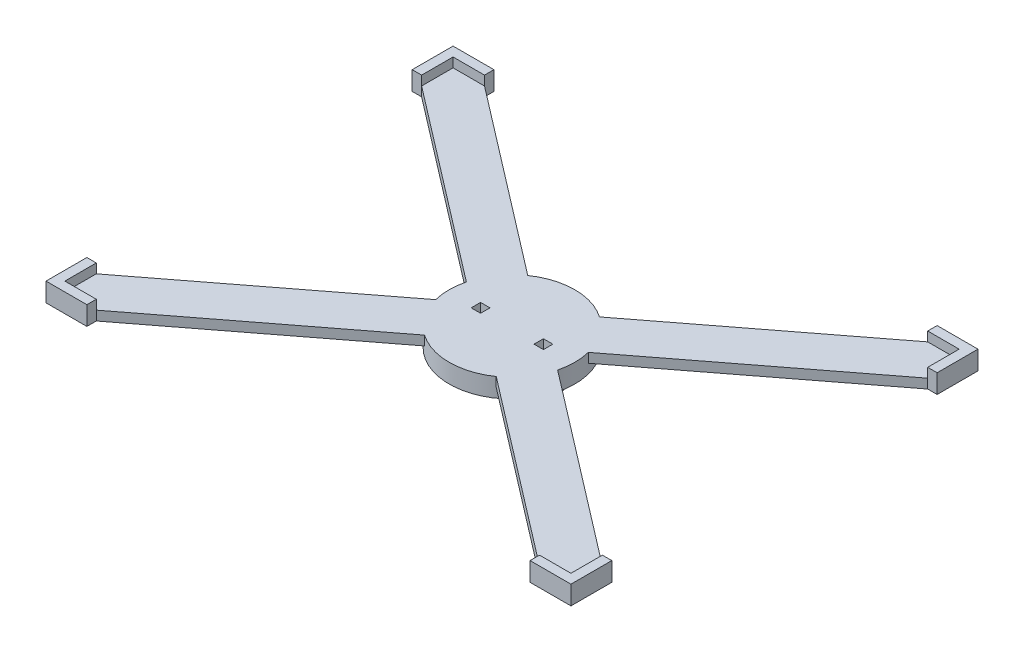
SolidWorks part; units mm, degrees
ref_plane "Alzado" through (0, 0, 0) normal (0, 0, 1) x (1, 0, 0)
ref_plane "Planta" through (0, 0, 0) normal (0, 1, 0) x (1, 0, 0)
ref_plane "Vista lateral" through (0, 0, 0) normal (1, 0, 0) x (0, 0, -1)
sketch "Croquis1" plane through (0, 0, 0) normal (0, 1, 0) x (1, 0, 0)
  line L0 (-161, 103.5) -> (-38.7919, 9.7565)
  line L1 (-40, 40) -> (40, 40) construction
  line L2 (-40, 40) -> (-40, -40) construction
  line L3 (-40, -40) -> (40, -40) construction
  line L4 (40, 40) -> (40, -40) construction
  line L5 (-40, 40) -> (40, -40) construction
  line L6 (-40, -40) -> (40, 40) construction
  line L7 (-161, 123.5) -> (161, 123.5) construction
  line L8 (-161, 123.5) -> (-161, -123.5) construction
  line L9 (-161, -123.5) -> (161, -123.5) construction
  line L10 (161, 123.5) -> (161, -123.5) construction
  line L11 (-161, 123.5) -> (161, -123.5) construction
  line L12 (-161, -123.5) -> (161, 123.5) construction
  line L13 (-161, 103.5) -> (-161, 123.5)
  line L14 (-161, 123.5) -> (-141, 123.5)
  line L15 (-141, 123.5) -> (-22.8238, 32.8493)
  line L16 (-38.7919, -9.7565) -> (-161, -103.5)
  line L17 (-161, -103.5) -> (-161, -123.5)
  line L18 (-161, -123.5) -> (-141, -123.5)
  line L19 (-141, -123.5) -> (-22.8238, -32.8493)
  line L20 (-38.7919, 9.7565) -> (-38.7919, -9.7565) construction
  line L21 (-22.8238, 32.8493) -> (-22.8238, -32.8493) construction
  line L22 (0, 40) -> (0, -40) construction
  line L23 (161, 123.5) -> (141, 123.5)
  line L24 (141, 123.5) -> (22.8238, 32.8493)
  line L25 (161, 103.5) -> (161, 123.5)
  line L26 (161, 103.5) -> (38.7919, 9.7565)
  line L27 (161, -123.5) -> (141, -123.5)
  line L28 (161, -103.5) -> (161, -123.5)
  line L29 (38.7919, -9.7565) -> (161, -103.5)
  line L30 (141, -123.5) -> (22.8238, -32.8493)
  circle A0 centre (0, 0) radius 40 construction
  arc A1 (-38.7919, 9.7565) -> (-38.7919, -9.7565) centre (0, 0) ccw
  arc A2 (-22.8238, 32.8493) -> (22.8238, 32.8493) centre (0, 0) cw
  arc A3 (22.8238, -32.8493) -> (-22.8238, -32.8493) centre (0, 0) cw
  arc A4 (38.7919, 9.7565) -> (38.7919, -9.7565) centre (0, 0) cw
  point P0 (0, 0)
  point P6 (0, 0)
  dimension "D1" = 80
  dimension "D2" = 80
  dimension "D3" = 322
  dimension "D4" = 247
  dimension "D5" = 20
extrude "Saliente-Extruir1" add sketch "Croquis1" along normal blind 6
sketch "Croquis4" plane through (0, 0, 0) normal (0, 1, 0) x (1, 0, 0)
  line L0 (-161, 103.5) -> (-161, 123.5)
  line L1 (-161, 123.5) -> (-141, 123.5)
  line L2 (-141, 123.5) -> (-141, 129.5)
  line L3 (-141, 129.5) -> (-167, 129.5)
  line L4 (-167, 129.5) -> (-167, 103.5)
  line L5 (-167, 103.5) -> (-161, 103.5)
  line L6 (-161, -103.5) -> (-161, -123.5)
  line L7 (-161, -123.5) -> (-141, -123.5)
  line L8 (-141, -123.5) -> (-141, -129.5)
  line L9 (-141, -129.5) -> (-167, -129.5)
  line L10 (-167, -129.5) -> (-167, -103.5)
  line L11 (-167, -103.5) -> (-161, -103.5)
  line L12 (0, 40) -> (0, -40) construction
  line L13 (167, -103.5) -> (161, -103.5)
  line L14 (167, -129.5) -> (167, -103.5)
  line L15 (141, -129.5) -> (167, -129.5)
  line L16 (141, -123.5) -> (141, -129.5)
  line L17 (161, -123.5) -> (141, -123.5)
  line L18 (161, -103.5) -> (161, -123.5)
  line L19 (167, 103.5) -> (161, 103.5)
  line L20 (167, 129.5) -> (167, 103.5)
  line L21 (141, 129.5) -> (167, 129.5)
  line L22 (141, 123.5) -> (141, 129.5)
  line L23 (161, 123.5) -> (141, 123.5)
  line L24 (161, 103.5) -> (161, 123.5)
  arc A0 (22.8238, 32.8493) -> (-22.8238, 32.8493) centre (0, 0) ccw construction
  arc A1 (-22.8238, -32.8493) -> (22.8238, -32.8493) centre (0, 0) ccw construction
  dimension "D1" = 6
  dimension "D2" = 6
  dimension "D3" = 6
  dimension "D4" = 6
extrude "Saliente-Extruir2" add sketch "Croquis4" along normal blind 12
sketch "Croquis7" plane through (0, 0, 0) normal (0, -1, 0) x (-1, 0, 0)
  circle A0 centre (0, 0) radius 40
  arc A1 (-38.7919, 9.7565) -> (-38.7919, -9.7565) centre (0, 0) ccw construction
extrude "Saliente-Extruir5" add sketch "Croquis7" along normal blind 6
sketch "Croquis5" plane through (0, -6, 0) normal (0, -1, 0) x (1, 0, 0)
  line L0 (13.25, 11) -> (-13.25, 11) construction
  line L1 (-10.25, 8) -> (10.25, 8) construction
  line L2 (-10.25, 8) -> (-10.25, -8) construction
  line L3 (-10.25, -8) -> (10.25, -8) construction
  line L4 (10.25, 8) -> (10.25, -8) construction
  line L5 (-10.25, 8) -> (10.25, -8) construction
  line L6 (-10.25, -8) -> (10.25, 8) construction
  line L7 (-13.25, 11) -> (-13.25, -11) construction
  line L8 (-13.25, -11) -> (13.25, -11) construction
  line L9 (13.25, -11) -> (13.25, -21) construction
  line L10 (13.25, -21) -> (-28.25, -21) construction
  line L11 (-28.25, -21) -> (-28.25, 21) construction
  line L12 (-28.25, 21) -> (13.25, 21) construction
  line L13 (13.25, 21) -> (13.25, 11) construction
  line L14 (0, 11) -> (0, 0) construction
  line L15 (0, 0) -> (0, -11) construction
  line L16 (13.25, 11) -> (28.25, 11) construction
  line L17 (-28.25, 21) -> (28.25, 21) construction
  line L18 (-28.25, 21) -> (-28.25, -21) construction
  line L19 (-28.25, -21) -> (28.25, -21) construction
  line L20 (28.25, 21) -> (28.25, -21) construction
  line L21 (-28.25, 21) -> (28.25, -21) construction
  line L22 (-28.25, -21) -> (28.25, 21) construction
  line L23 (28.25, 11) -> (28.25, 21) construction
  line L24 (28.25, 21) -> (13.25, 21) construction
  line L25 (13.25, -21) -> (28.25, -21) construction
  line L26 (28.25, -21) -> (28.25, -11) construction
  line L27 (28.25, -11) -> (13.25, -11) construction
  line L28 (-9, 7) -> (9, 7) construction
  line L29 (0, 7) -> (0, 0) construction
  line L30 (-9, 7) -> (9, 7) construction
  line L31 (-9, 7.5) -> (9, 7.5) construction
  line L32 (-9, 6.5) -> (9, 6.5) construction
  line L33 (-18.8961, 21) -> (18.8961, 21) construction
  line L34 (18.8961, -21) -> (-18.8961, -21)
  line L35 (-18.8961, 21) -> (-13.25, 21)
  line L36 (-13.25, 21) -> (-13.25, -11)
  line L37 (-13.25, -11) -> (13.25, -11)
  line L38 (13.25, -11) -> (13.25, 21)
  line L39 (13.25, 21) -> (18.8961, 21)
  line L40 (-8, -5.75) -> (8, -5.75) construction
  arc A0 (-9, 7.5) -> (-9, 6.5) centre (-9, 7) ccw construction
  arc A1 (9, 6.5) -> (9, 7.5) centre (9, 7) ccw construction
  arc A2 (-18.8961, 21) -> (-18.8961, -21) centre (0, 0) ccw
  arc A3 (18.8961, 21) -> (18.8961, -21) centre (0, 0) cw
  circle A4 centre (-8, -5.75) radius 1.75 construction
  circle A5 centre (8, -5.75) radius 1.75 construction
  point P0 (0, 0)
  point P26 (0, 7)
  dimension "D11" = 0.5
  dimension "D12" = 3.5
  dimension "D14" = 2.25
  dimension "D1" = 16
  dimension "D2" = 20.5
  dimension "D3" = 3
  dimension "D4" = 3
  dimension "D5" = 10
  dimension "D6" = 10
  dimension "D7" = 15
  dimension "D8" = 3
  dimension "D9" = 18
  dimension "D10" = 1
  dimension "D13" = 2.25
  dimension "D15" = 2.25
extrude "Saliente-Extruir3" add sketch "Croquis5" along normal blind 6
sketch "Croquis6" plane through (0, -12, 0) normal (0, -1, 0) x (1, 0, 0)
  line L0 (18.8961, 21) -> (13.25, 21) construction
  line L1 (-28.25, 21) -> (28.25, 21) construction
  line L2 (-28.25, 21) -> (-28.25, -21) construction
  line L3 (-28.25, -21) -> (28.25, -21) construction
  line L4 (28.25, 21) -> (28.25, -21) construction
  line L5 (-28.25, 21) -> (28.25, -21) construction
  line L6 (-28.25, -21) -> (28.25, 21) construction
  line L7 (-18.8961, 21) -> (-13.25, 21)
  line L8 (-9, 7) -> (9, 7) construction
  line L9 (-9, 7.5) -> (9, 7.5) construction
  line L10 (-9, 6.5) -> (9, 6.5) construction
  line L11 (-18.8961, 21) -> (18.8961, 21) construction
  line L12 (18.8961, -21) -> (-18.8961, -21) construction
  line L18 (13.25, 21) -> (18.8961, 21)
  line L19 (18.8961, -21) -> (-18.8961, -21)
  line L20 (-13.25, 21) -> (-13.25, 3.5)
  line L21 (-13.25, 21) -> (-13.25, -11) construction
  line L22 (-12.75, 3) -> (12.75, 3)
  line L23 (13.25, -11) -> (13.25, 21) construction
  line L24 (13.25, 3.5) -> (13.25, 21)
  line L25 (-13.25, 3.5) -> (13.25, 3.5) construction
  arc A0 (-9, 7.5) -> (-9, 6.5) centre (-9, 7) ccw construction
  arc A1 (9, 6.5) -> (9, 7.5) centre (9, 7) ccw construction
  arc A2 (9, 6.5) -> (9, 7.5) centre (9, 7) ccw construction
  circle A3 centre (0, 0) radius 28.25 construction
  arc A4 (18.8961, 21) -> (18.8961, -21) centre (0, 0) cw construction
  arc A5 (-18.8961, -21) -> (-18.8961, 21) centre (0, 0) cw construction
  arc A6 (-18.8961, 21) -> (-18.8961, -21) centre (0, 0) ccw construction
  arc A7 (-18.8961, -21) -> (-18.8961, 21) centre (0, 0) cw
  arc A8 (18.8961, -21) -> (18.8961, 21) centre (0, 0) ccw
  circle A9 centre (-8, -5.75) radius 1.75
  circle A10 centre (8, -5.75) radius 1.75
  circle A11 centre (-8, -5.75) radius 1.75 construction
  circle A12 centre (8, -5.75) radius 1.75 construction
  arc A13 (-13.25, 3.5) -> (-12.75, 3) centre (-12.75, 3.5) ccw
  arc A14 (12.75, 3) -> (13.25, 3.5) centre (12.75, 3.5) ccw
  point P0 (0, 0)
  point P14 (0, 7)
  dimension "D2" = 0.5
  dimension "D1" = 18
extrude "Saliente-Extruir4" add sketch "Croquis6" along normal blind 6
sketch "Croquis8" plane through (0, -18, 0) normal (0, -1, 0) x (1, 0, 0)
  line L0 (-20, 0) -> (0, 0) construction
  line L1 (-23, 3) -> (-17, 3)
  line L2 (-23, 3) -> (-23, -3)
  line L3 (-23, -3) -> (-17, -3)
  line L4 (-17, 3) -> (-17, -3)
  line L5 (-23, 3) -> (-17, -3) construction
  line L6 (-23, -3) -> (-17, 3) construction
  line L7 (0, 0) -> (0, -21) construction
  line L8 (-18.8961, -21) -> (18.8961, -21) construction
  line L9 (23, -3) -> (17, -3)
  line L10 (23, 3) -> (23, -3)
  line L11 (23, 3) -> (17, 3)
  line L12 (17, 3) -> (17, -3)
  point P0 (-20, 0)
  dimension "D1" = 6
  dimension "D2" = 6
  dimension "D3" = 20
extrude "Cortar-Extruir1" cut sketch "Croquis8" against normal through all
